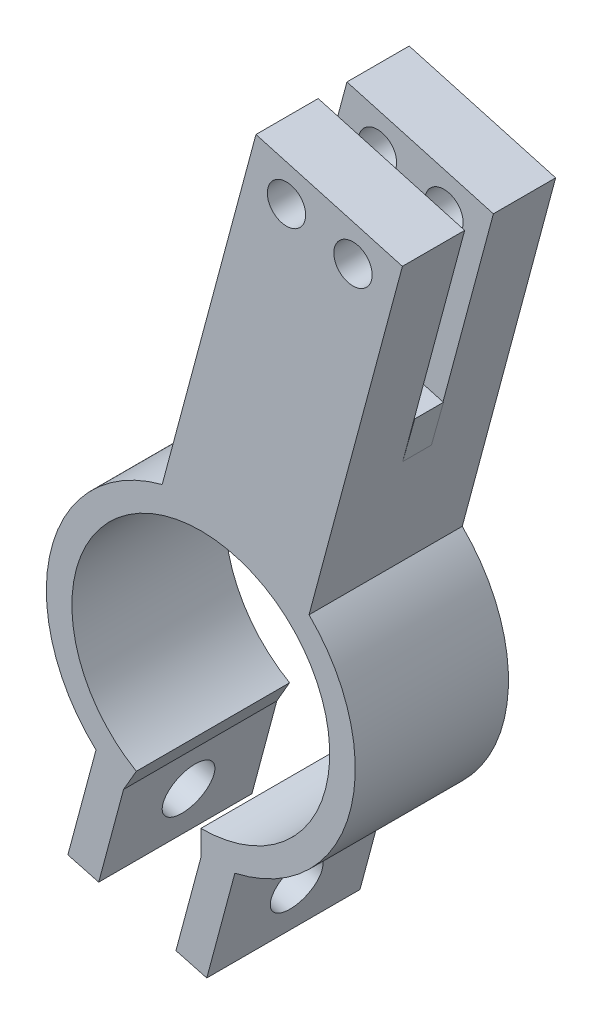
SolidWorks part; units mm, degrees
ref_plane "Front Plane" through (0, 0, 0) normal (0, 0, 1) x (1, 0, 0)
ref_plane "Top Plane" through (0, 0, 0) normal (0, 1, 0) x (1, 0, 0)
ref_plane "Right Plane" through (0, 0, 0) normal (1, 0, 0) x (0, 0, -1)
sketch "Sketch1" plane through (0, 0, 0) normal (0, 0, 1) x (1, 0, 0)
  circle A0 centre (0, 0) radius 20.193
  circle A1 centre (0, 0) radius 20.193 construction
  circle A2 centre (0, 0) radius 24.193
  dimension "D1" = 4
extrude "Boss-Extrude1" add sketch "Sketch1" along normal blind 24
sketch "Sketch2" plane through (0, 0, 24) normal (0, 0, 1) x (1, 0, 0)
  line L0 (0, -24.193) -> (-5.8342, -24.8953)
  line L1 (-5.8342, -24.8953) -> (-12.0965, -20.9518)
  line L2 (0, -24.193) -> (0, 0)
  line L3 (-12.0965, -20.9518) -> (0, 0)
  circle A0 centre (0, 0) radius 24.193 construction
  dimension "D1" = 7.4005
  dimension "D2" = 5.8342
  dimension "D3" = 30
extrude "Cut-Extrude1" cut sketch "Sketch2" against normal blind 24
sketch "Sketch3" plane through (0, 0, 24) normal (0, 0, 1) x (1, 0, 0)
  line L0 (-12.0965, -20.9518) -> (-15.99, -35.4826)
  line L1 (-15.99, -35.4826) -> (-20.8197, -34.1885)
  line L2 (-20.8197, -34.1885) -> (-16.4197, -17.7678)
  line L3 (-12.0965, -20.9518) -> (-16.4197, -17.7678)
  line L4 (0, -24.193) -> (5.336, -23.5972)
  line L5 (5.336, -23.5972) -> (0.9361, -40.0179)
  line L6 (0.9361, -40.0179) -> (-3.8935, -38.7238)
  line L7 (-3.8935, -38.7238) -> (0, -24.193)
  line L8 (-3.8935, -38.7238) -> (-15.99, -35.4826)
  line L9 (0, -24.193) -> (-12.0965, -20.9518)
  arc A0 (0, -24.193) -> (-12.0965, -20.9518) centre (0, 0) ccw construction
  arc M6 (0, -24.193) -> (-12.0965, -20.9518) centre (0, 0) ccw
  dimension "D1" = 17
  dimension "D2" = 5
extrude "Boss-Extrude2" add sketch "Sketch3" against normal blind 24 contours L2 L1 L0 M6 | L7 L6 L5 M6
sketch "Sketch4" plane through (-10.8779, 2.9147, 0) normal (-0.9659, 0.2588, 0) x (0, 0, 1)
  line L0 (12, -38.4121) -> (12, -30.4121)
  line L1 (0, -38.4121) -> (24, -38.4121) construction
  circle A0 centre (12, -30.4121) radius 4
  dimension "D2" = 8
  dimension "D1" = 8
extrude "Cut-Extrude2" cut sketch "Sketch4" against normal blind 24
sketch "Sketch5" plane through (0, 0, 24) normal (0, 0, 1) x (1, 0, 0)
  line L0 (0, -20.193) -> (-10.0965, -17.4877)
  line L3 (16.9534, 17.2593) -> (31.5792, 71.8436)
  line L4 (31.5792, 71.8436) -> (8.6406, 78.2587)
  line L5 (8.6406, 78.2587) -> (-6.0524, 23.4237)
  line L6 (16.9534, 17.2593) -> (-6.0524, 23.4237)
  line L7 (20.1099, 75.0512) -> (18.6286, 69.7544)
  line L8 (13.4213, 71.2107) -> (18.6286, 69.7544)
  line L9 (18.6286, 69.7544) -> (23.8359, 68.2981)
  line L10 (5.6922, 67.2554) -> (28.6981, 61.091)
  arc A0 (5.336, -23.5972) -> (-16.4197, -17.7678) centre (0, 0) ccw construction
  circle A2 centre (23.8359, 68.2981) radius 3
  circle A3 centre (13.4213, 71.2107) radius 3
  dimension "D1" = 6
  dimension "D4" = 6
  dimension "D2" = 23.8188
  dimension "D3" = 40.564
  dimension "D5" = 5.5
  dimension "D6" = 5.4071
  dimension "D7" = 56.5098
  dimension "D8" = 45.3779
extrude "Boss-Extrude3" add sketch "Sketch5" against normal blind 24
sketch "Sketch6" plane through (20.9253, 74.8231, 0) normal (0.2693, 0.963, 0) x (0.963, -0.2693, 0)
  line L0 (-12.7561, 0) -> (-12.7561, -24) construction
  line L1 (-12.7561, -9.75) -> (11.0627, -9.75)
  line L2 (-12.7561, -9.75) -> (-12.7561, -14.25)
  line L3 (-12.7561, -14.25) -> (11.0627, -14.25)
  line L4 (11.0627, -9.75) -> (11.0627, -14.25)
  line L5 (11.0627, 0) -> (11.0627, -24) construction
  line L6 (-0.8467, 0) -> (-0.8467, -9.75)
  line L7 (11.0627, 0) -> (-12.7561, 0) construction
  line L8 (-0.8467, -14.25) -> (-0.8467, -24)
  line L9 (11.0627, -24) -> (-12.7561, -24) construction
  line M8 (11.0627, -24) -> (11.0627, 0)
  line M10 (-12.7561, 0) -> (-12.7561, -24)
  dimension "D1" = 4.5
extrude "Cut-Extrude3" cut sketch "Sketch6" against normal blind 37 contours L3 L1 M10 M8
sketch "Sketch7" plane through (11.5029, -3.0822, 0) normal (0.9659, -0.2588, 0) x (0, 0, -1)
  line L5 (-14.25, 77.5689) -> (-9.75, 77.5689)
  line L6 (-14.25, 77.5689) -> (-14.25, 40.0689)
  line L7 (-14.25, 40.0689) -> (-9.75, 40.0689)
  line L8 (-9.75, 77.5689) -> (-9.75, 40.0689)
  dimension "D1" = 37.5
  dimension "D2" = 4.5
extrude "Cut-Extrude4" cut sketch "Sketch7" against normal blind 0.5
sketch "Sketch8" plane through (10.9601, 39.1903, 0) normal (0.2693, 0.963, 0) x (0.963, -0.2693, 0)
  line L1 (-12.3529, -9.75) -> (11.4714, -9.75)
  line L2 (-12.3529, -9.75) -> (-12.3529, -14.25)
  line L3 (-12.3529, -14.25) -> (11.4714, -14.25)
  line L4 (11.4714, -9.75) -> (11.4714, -14.25)
  point P5 (0, 0)
extrude "Boss-Extrude4" add sketch "Sketch8" along normal blind 6.5 and the other way blind 1
